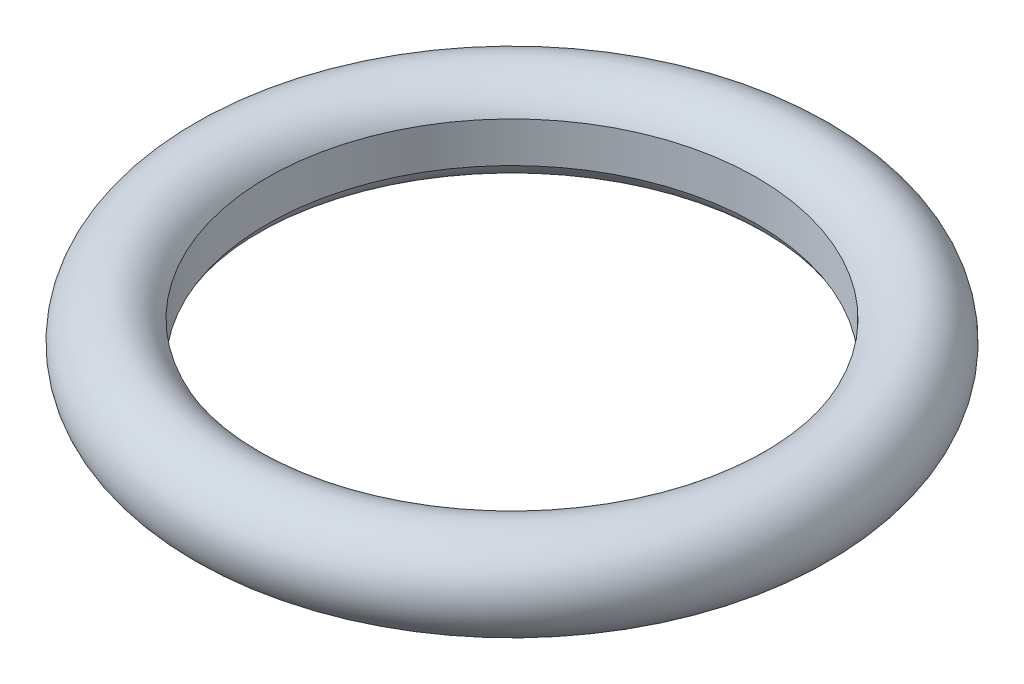
SolidWorks part; units mm, degrees
ref_plane "Front Plane" through (0, 0, 0) normal (0, 0, 1) x (1, 0, 0)
ref_plane "Top Plane" through (0, 0, 0) normal (0, 1, 0) x (1, 0, 0)
ref_plane "Right Plane" through (0, 0, 0) normal (1, 0, 0) x (0, 0, -1)
sketch "Sketch1" plane through (0, 0, 0) normal (0, 0, 1) x (1, 0, 0)
  line L0 (0, 0) -> (-5.6439, 0) construction
  line L1 (0, 0) -> (0, 21.5583) construction
  line L2 (-4.85, 0.4) -> (-4.85, -0.4)
  arc A0 (-4.85, 0.4) -> (-4.85, -0.4) centre (-5.6439, 0) ccw
  dimension "D1" = 1.778
  dimension "D2" = 4.85
  dimension "D3" = 0.8
revolve "Revolve1" add sketch "Sketch1" angle 360 about L1
